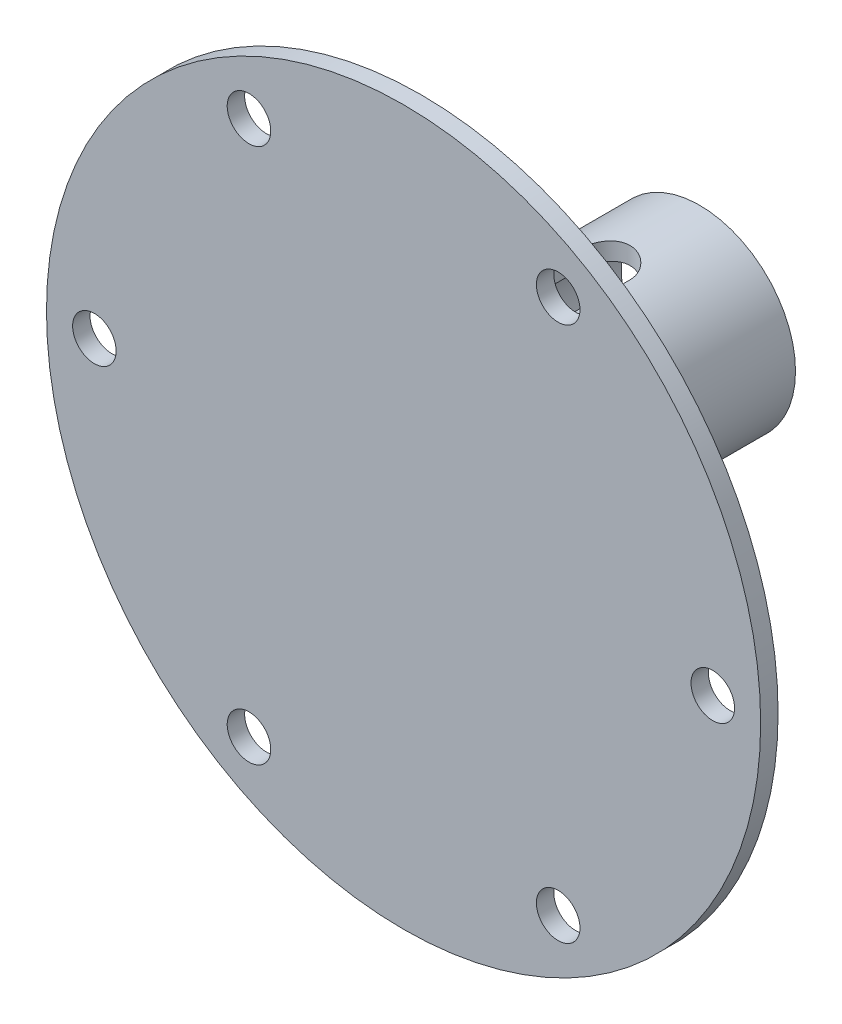
SolidWorks part; units mm, degrees
ref_plane "Ön Düzlem" through (0, 0, 0) normal (0, 0, 1) x (1, 0, 0)
ref_plane "Üst Düzlem" through (0, 0, 0) normal (0, 1, 0) x (1, 0, 0)
ref_plane "Sağ Düzlem" through (0, 0, 0) normal (1, 0, 0) x (0, 0, -1)
sketch "Sketch1" plane through (0, 0, 0) normal (0, 0, 1) x (1, 0, 0)
  circle A0 centre (0, 0) radius 6 construction
  circle A1 centre (0, 3) radius 9
  circle A2 centre (0, 3) radius 11
  dimension "D1" = 12
  dimension "D2" = 22
  dimension "D3" = 18
extrude "Boss-Extrude1" add sketch "Sketch1" against normal blind 32
sketch "Sketch2" plane through (0, 0, 0) normal (0, 1, 0) x (1, 0, 0)
  line L0 (0, 21) -> (0, 6) construction
  line L1 (3, 21) -> (3, 6)
  line L2 (-3, 21) -> (-3, 6)
  line L3 (-11, 0) -> (11, 0) construction
  arc A0 (3, 21) -> (-3, 21) centre (0, 21) ccw
  arc A1 (-3, 6) -> (3, 6) centre (0, 6) ccw
  point P3 (0, 13.5)
  dimension "D1" = 6
  dimension "D2" = 6
  dimension "D3" = 15
extrude "Cut-Extrude1" cut sketch "Sketch2" against normal through all both and the other way through all
sketch "Sketch3" plane through (0, 0, 0) normal (0, 0, 1) x (1, 0, 0)
  circle A0 centre (0, 0) radius 41
  dimension "D1" = 82
extrude "Boss-Extrude2" add sketch "Sketch3" along normal blind 2
fillet "Fillet1" radius 2 1 edges at (11, 3, 0)
sketch "Sketch4" plane through (0, 0, 2) normal (0, 0, 1) x (1, 0, 0)
  circle A0 centre (0, 0) radius 35.5 construction
  circle A1 centre (35.5, 0) radius 2.5
  circle A2 centre (17.75, -30.7439) radius 2.5
  circle A3 centre (-17.75, -30.7439) radius 2.5
  circle A4 centre (-35.5, 0) radius 2.5
  circle A5 centre (-17.75, 30.7439) radius 2.5
  circle A6 centre (17.75, 30.7439) radius 2.5
  point P17 (0, 0)
  dimension "D1" = 71
  dimension "D2" = 5
  dimension "D3" = 6
extrude "Cut-Extrude2" cut sketch "Sketch4" against normal blind 2
